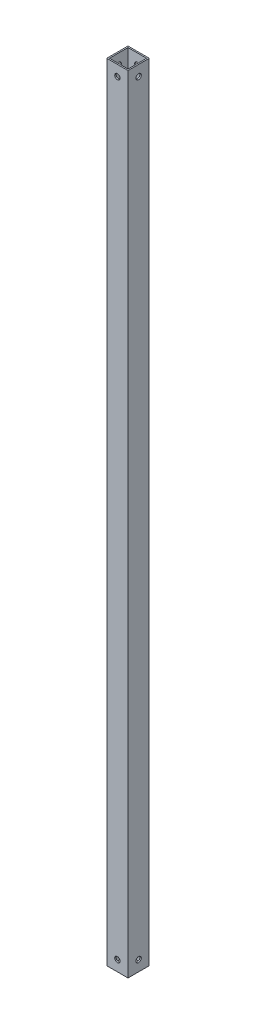
SolidWorks part; units mm, degrees
ref_plane "Front Plane" through (0, 0, 0) normal (0, 0, 1) x (1, 0, 0)
ref_plane "Top Plane" through (0, 0, 0) normal (0, 1, 0) x (1, 0, 0)
ref_plane "Right Plane" through (0, 0, 0) normal (1, 0, 0) x (0, 0, -1)
sketch "Sketch1" plane through (0, 0, 0) normal (0, 1, 0) x (1, 0, 0)
  line L0 (-11.1125, 11.1125) -> (11.1125, 11.1125)
  line L1 (-12.7, 12.7) -> (12.7, 12.7)
  line L2 (-12.7, 12.7) -> (-12.7, -12.7)
  line L3 (-12.7, -12.7) -> (12.7, -12.7)
  line L4 (12.7, 12.7) -> (12.7, -12.7)
  line L5 (-12.7, 12.7) -> (12.7, -12.7) construction
  line L6 (-12.7, -12.7) -> (12.7, 12.7) construction
  line L11 (11.1125, 11.1125) -> (11.1125, -11.1125)
  line L12 (-11.1125, -11.1125) -> (11.1125, -11.1125)
  line L13 (-11.1125, 11.1125) -> (-11.1125, -11.1125)
  point P0 (0, 0)
  dimension "D1" = 25.4
  dimension "D2" = 25.4
  dimension "D3" = 1.5875
extrude "Boss-Extrude1" add sketch "Sketch1" along normal blind 939.8
sketch "Sketch2" plane through (12.7, 0, 0) normal (1, 0, 0) x (0, 0, -1)
  line L0 (-12.7, 939.8) -> (-12.7, 0) construction
  line L1 (-12.7, 0) -> (12.7, 0) construction
  line L2 (-12.7, 939.8) -> (12.7, 939.8) construction
  line L3 (12.7, 939.8) -> (12.7, 0) construction
  circle A0 centre (0, 12.7) radius 3.175
  circle A1 centre (0, 927.1) radius 3.175
  dimension "D3" = 6.35
  dimension "D5" = 6.35
  dimension "D1" = 12.7
  dimension "D2" = 12.7
  dimension "D4" = 12.7
  dimension "D6" = 12.7
extrude "Cut-Extrude1" cut sketch "Sketch2" against normal through all
sketch "Sketch3" plane through (0, 0, 12.7) normal (0, 0, 1) x (1, 0, 0)
  line L0 (-12.7, 939.8) -> (-12.7, 0) construction
  line L1 (-12.7, 0) -> (12.7, 0) construction
  line L2 (-12.7, 939.8) -> (12.7, 939.8) construction
  line L3 (12.7, 939.8) -> (12.7, 0) construction
  circle A0 centre (0, 12.7) radius 3.175
  circle A1 centre (0, 927.1) radius 3.175
  dimension "D3" = 6.35
  dimension "D6" = 6.35
  dimension "D1" = 12.7
  dimension "D2" = 12.7
  dimension "D4" = 12.7
  dimension "D5" = 12.7
extrude "Cut-Extrude2" cut sketch "Sketch3" against normal through all
